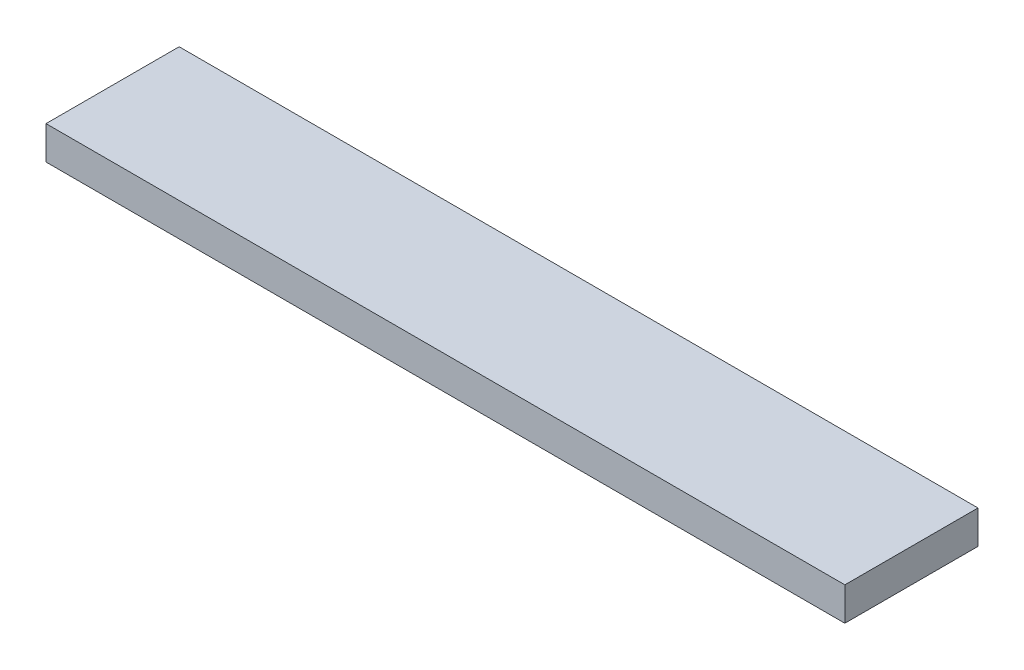
SolidWorks part; units mm, degrees
ref_plane "Front Plane" through (0, 0, 0) normal (0, 0, 1) x (1, 0, 0)
ref_plane "Top Plane" through (0, 0, 0) normal (0, 1, 0) x (1, 0, 0)
ref_plane "Right Plane" through (0, 0, 0) normal (1, 0, 0) x (0, 0, -1)
sketch "Sketch1" plane through (0, 0, 0) normal (0, 1, 0) x (1, 0, 0)
  line L1 (0, 0) -> (76.2, 0)
  line L2 (0, 0) -> (0, -12.7)
  line L3 (0, -12.7) -> (76.2, -12.7)
  line L4 (76.2, 0) -> (76.2, -12.7)
extrude "Boss-Extrude1" add sketch "Sketch1" along normal blind 3.175
